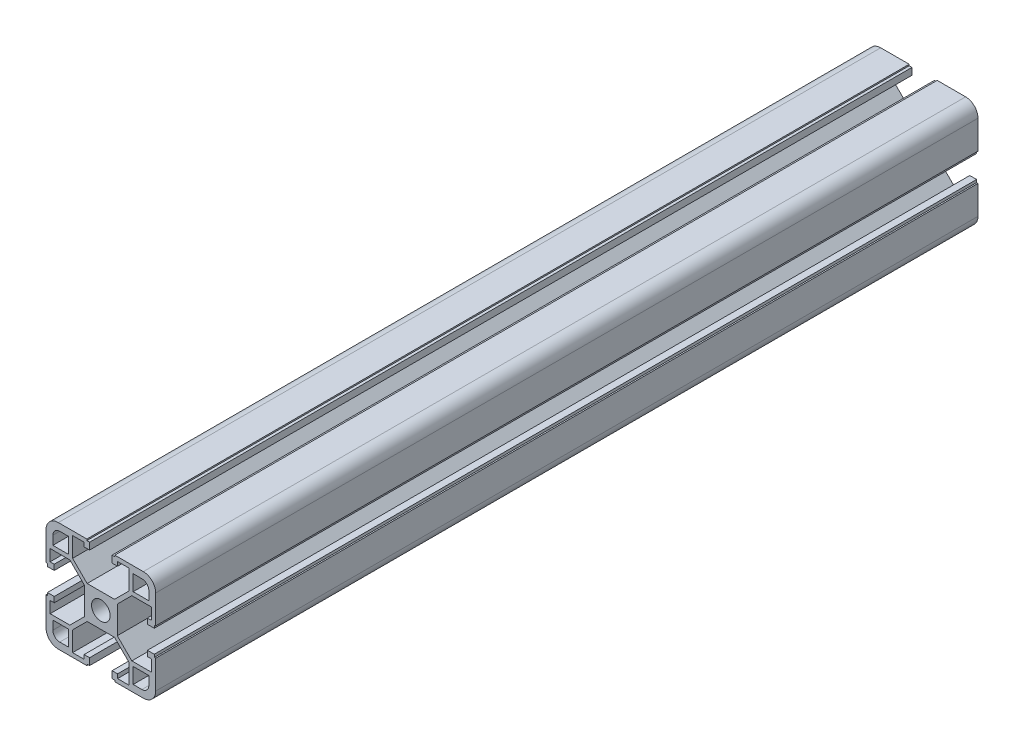
SolidWorks part; units mm, degrees
ref_plane "前视基准面" through (0, 0, 0) normal (0, 0, 1) x (1, 0, 0)
ref_plane "上视基准面" through (0, 0, 0) normal (0, 1, 0) x (1, 0, 0)
ref_plane "右视基准面" through (0, 0, 0) normal (1, 0, 0) x (0, 0, -1)
sketch "草图1" plane through (0, 0, 0) normal (0, 1, 0) x (1, 0, 0)
  line L0 (0, 151.8072) -> (0, -148.1928)
  dimension "D1" = 300
other "铝型材 40 X 40L X R4.5(1)"
ref_plane "基准面1" through (0, 0, -151.8072) normal (0, 0, 1) x (1, 0, 0)
sketch "Sketch1" plane through (0, 0, -151.8072) normal (0, 0, 1) x (1, 0, 0)
  line L0 (-5.1, 20) -> (-5.1, 19.5)
  line L1 (-5.1, 19.5) -> (-4.1, 19.5)
  line L2 (-4.1, 19.5) -> (-4.1, 17)
  line L3 (-6.1, 18.5) -> (-10.3, 18.5)
  line L4 (-15.5, -20) -> (-5.1, -20)
  line L5 (-20, -15.5) -> (-20, -5.1)
  line L6 (15.5, 20) -> (5.1, 20)
  line L7 (20, 15.5) -> (20, 5.1)
  line L8 (0, 14.8756) -> (0, 0) construction
  line L9 (0, 0) -> (14.1675, 0) construction
  line L10 (-10.3, 18.5) -> (-10.3, 11.3)
  line L11 (-10.3, 11.3) -> (-5, 6)
  line L12 (-5, 6) -> (5, 6)
  line L13 (10.3, 11.3) -> (5, 6)
  line L14 (10.3, 18.5) -> (10.3, 11.3)
  line L15 (6.1, 18.5) -> (10.3, 18.5)
  line L16 (4.1, 19.5) -> (4.1, 17)
  line L17 (5.1, 19.5) -> (4.1, 19.5)
  line L18 (5.1, 20) -> (5.1, 19.5)
  line L19 (-5.1, 20) -> (-15.5, 20)
  line L20 (20, 5.1) -> (19.5, 5.1)
  line L21 (11.8, 17.5) -> (15, 17.5)
  line L22 (11.8, 17.5) -> (11.8, 11.8)
  line L23 (11.8, 11.8) -> (17.5, 11.8)
  line L24 (17.5, 15) -> (17.5, 11.8)
  line L25 (19.5, 5.1) -> (19.5, 4.1)
  line L26 (19.5, 4.1) -> (17, 4.1)
  line L27 (17, 6.1) -> (17, 4.1)
  line L28 (18.5, 6.1) -> (17, 6.1)
  line L29 (18.5, 6.1) -> (18.5, 10.3)
  line L30 (18.5, 10.3) -> (11.3, 10.3)
  line L31 (11.3, 10.3) -> (6, 5)
  line L32 (6, 5) -> (6, -5)
  line L33 (11.3, -10.3) -> (6, -5)
  line L34 (18.5, -10.3) -> (11.3, -10.3)
  line L35 (18.5, -6.1) -> (18.5, -10.3)
  line L36 (18.5, -6.1) -> (17, -6.1)
  line L37 (17, -4.1) -> (17, -6.1)
  line L38 (19.5, -4.1) -> (17, -4.1)
  line L39 (19.5, -5.1) -> (19.5, -4.1)
  line L40 (20, -5.1) -> (19.5, -5.1)
  line L41 (5.1, -20) -> (5.1, -19.5)
  line L42 (5.1, -19.5) -> (4.1, -19.5)
  line L43 (4.1, -19.5) -> (4.1, -17)
  line L44 (6.1, -17) -> (4.1, -17)
  line L45 (6.1, -18.5) -> (6.1, -17)
  line L46 (6.1, -18.5) -> (10.3, -18.5)
  line L47 (10.3, -18.5) -> (10.3, -11.3)
  line L48 (10.3, -11.3) -> (5, -6)
  line L49 (5, -6) -> (-5, -6)
  line L50 (-10.3, -11.3) -> (-5, -6)
  line L51 (-10.3, -18.5) -> (-10.3, -11.3)
  line L52 (-6.1, -18.5) -> (-10.3, -18.5)
  line L53 (-6.1, -18.5) -> (-6.1, -17)
  line L54 (-4.1, -17) -> (-6.1, -17)
  line L55 (-4.1, -19.5) -> (-4.1, -17)
  line L56 (-5.1, -19.5) -> (-4.1, -19.5)
  line L57 (-5.1, -20) -> (-5.1, -19.5)
  line L58 (-20, -5.1) -> (-19.5, -5.1)
  line L59 (5.1, -20) -> (15.5, -20)
  line L60 (-20, 5.1) -> (-20, 15.5)
  line L61 (-19.5, -5.1) -> (-19.5, -4.1)
  line L62 (-6.1, 18.5) -> (-6.1, 17)
  line L63 (-6.1, 17) -> (-4.1, 17)
  line L64 (6.1, 18.5) -> (6.1, 17)
  line L65 (4.1, 17) -> (6.1, 17)
  line L66 (-19.5, -4.1) -> (-17, -4.1)
  line L67 (-15, 17.5) -> (-11.8, 17.5)
  line L68 (-17.5, 15) -> (-17.5, 11.8)
  line L69 (-17.5, 11.8) -> (-11.8, 11.8)
  line L70 (-11.8, 17.5) -> (-11.8, 11.8)
  line L71 (-17, -6.1) -> (-17, -4.1)
  line L72 (-18.5, -6.1) -> (-17, -6.1)
  line L73 (-18.5, -6.1) -> (-18.5, -10.3)
  line L74 (-18.5, -10.3) -> (-11.3, -10.3)
  line L75 (-11.3, -10.3) -> (-6, -5)
  line L76 (-6, -5) -> (-6, 5)
  line L77 (-11.3, 10.3) -> (-6, 5)
  line L78 (-18.5, 10.3) -> (-11.3, 10.3)
  line L79 (-18.5, 6.1) -> (-18.5, 10.3)
  line L80 (-18.5, 6.1) -> (-17, 6.1)
  line L81 (-17, 4.1) -> (-17, 6.1)
  line L82 (-19.5, 4.1) -> (-17, 4.1)
  line L83 (-19.5, 5.1) -> (-19.5, 4.1)
  line L84 (-20, 5.1) -> (-19.5, 5.1)
  line L85 (20, -5.1) -> (20, -15.5)
  line L87 (-17.5, -11.8) -> (-11.8, -11.8)
  line L88 (-17.5, -11.8) -> (-17.5, -15)
  line L89 (-15, -17.5) -> (-11.8, -17.5)
  line L90 (-11.8, -11.8) -> (-11.8, -17.5)
  line L91 (11.8, -11.8) -> (17.5, -11.8)
  line L92 (11.8, -11.8) -> (11.8, -17.5)
  line L93 (11.8, -17.5) -> (15, -17.5)
  line L94 (17.5, -11.8) -> (17.5, -15)
  circle A0 centre (0, 0) radius 3.4
  arc A1 (-20, 15.5) -> (-15.5, 20) centre (-15.5, 15.5) cw
  arc A2 (20, 15.5) -> (15.5, 20) centre (15.5, 15.5) ccw
  arc A3 (-15.5, -20) -> (-20, -15.5) centre (-15.5, -15.5) cw
  arc A4 (15.5, -20) -> (20, -15.5) centre (15.5, -15.5) ccw
  arc A5 (-15, 17.5) -> (-17.5, 15) centre (-15, 15) ccw
  arc A6 (17.5, 15) -> (15, 17.5) centre (15, 15) ccw
  arc A7 (17.5, -15) -> (15, -17.5) centre (15, -15) cw
  arc A8 (-17.5, -15) -> (-15, -17.5) centre (-15, -15) ccw
  point P2 (0, 10)
  point P4 (0, 0)
  point P5 (-20, -20)
  point P6 (20, -20)
  point P7 (20, 20)
  point P8 (-20, 20)
  point P36 (-20, 20)
  point P39 (20, 20)
  point P121 (0, 0)
  dimension "D1" = 20.6
  dimension "D2" = 40
  dimension "D3" = 8.2
  dimension "D4" = 10.2
  dimension "D5" = 14
  dimension "D6" = 6.8
  dimension "D7" = 4.5
  dimension "D8" = 45
  dimension "D12" = 2.5
  dimension "D13" = 5.7
  dimension "D14" = 1.5
  dimension "D18" = 2.5
  dimension "D19" = 2.5
  dimension "D15" = 2.5
  dimension "D9" = 0.5
  dimension "D10" = 1.5
  dimension "D11" = 10
  dimension "D16" = 3
  dimension "D17" = 2
  dimension "D20" = 1.5
  dimension "D21" = 2.5
